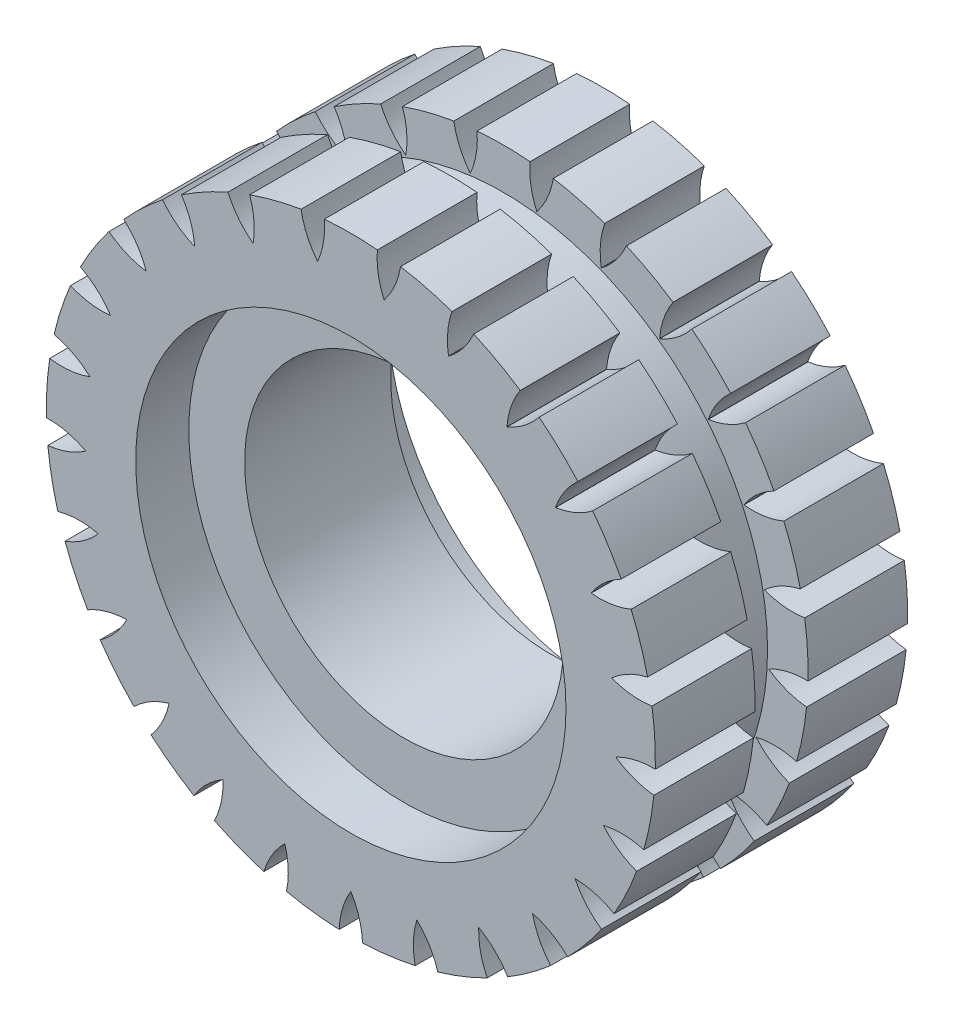
SolidWorks part; units mm, degrees
ref_plane "Ebene vorne" through (0, 0, 0) normal (0, 0, 1) x (1, 0, 0)
ref_plane "Ebene oben" through (0, 0, 0) normal (0, 1, 0) x (1, 0, 0)
ref_plane "Ebene rechts" through (0, 0, 0) normal (1, 0, 0) x (0, 0, -1)
sketch "Skizze1" plane through (0, 0, 0) normal (1, 0, 0) x (0, 0, -1)
  line L0 (-5.5, 0) -> (5.5, 0)
  line L1 (-19.3304, -12) -> (21.4195, -12) construction
  line L2 (0, 0) -> (0, 8) construction
  line L3 (-5.5, 0) -> (-5.5, 4.2)
  line L4 (-5.5, 4.2) -> (-9.5, 4.2)
  line L5 (-9.5, 4.2) -> (-9.5, 8)
  line L6 (-9.5, 8) -> (9.5, 8)
  line L7 (9.5, 4.2) -> (9.5, 8)
  line L8 (5.5, 4.2) -> (9.5, 4.2)
  line L9 (5.5, 0) -> (5.5, 4.2)
  dimension "D1" = 4.2
  dimension "D2" = 3.8
  dimension "D3" = 11
  dimension "D4" = 4
  dimension "D5" = 40
revolve "Rotation1" add sketch "Skizze1" angle 360 about L1
sketch "Skizze2" plane through (0, 0, 9.5) normal (0, 0, 1) x (1, 0, 0)
  line L1 (0, 18.2198) -> (0, 8) construction
  line L2 (0, 8) -> (0, -12) construction
  line L3 (-2, 10.8431) -> (-3.3426, 26.1783) construction
  line L5 (-14.9244, 9.7116) -> (-2, 10.8431) construction
  circle A1 centre (0, -12) radius 20 construction
  arc A76 (-2.5, 7.8431) -> (2.5, 7.8431) centre (0, -12) cw
  arc A77 (-2.5, 7.8431) -> (-2, 10.8431) centre (-8.0643, 10.3122) ccw
  arc A78 (-2, 10.8431) -> (2, 10.8431) centre (0, -12) cw
  arc A79 (2.5, 7.8431) -> (2, 10.8431) centre (8.0643, 10.3122) cw
  arc A80 (3.7437, 10.6229) -> (7.618, 9.6281) centre (0, -12) cw
  arc A81 (2.5133, 7.8415) -> (3.7437, 10.6229) centre (-2.2621, 11.6167) ccw
  arc A82 (2.5133, 7.8415) -> (7.3562, 6.598) centre (0, -12) cw
  arc A83 (7.3562, 6.598) -> (7.618, 9.6281) centre (13.3598, 7.6057) cw
  arc A84 (9.2522, 8.9811) -> (12.7574, 7.0541) centre (0, -12) cw
  arc A85 (7.3687, 6.5931) -> (9.2522, 8.9811) centre (3.6822, 11.4373) ccw
  arc A86 (7.3687, 6.5931) -> (11.7503, 4.1843) centre (0, -12) cw
  arc A87 (11.7503, 4.1843) -> (12.7574, 7.0541) centre (17.8158, 3.6673) cw
  arc A88 (14.1793, 6.021) -> (17.0951, 3.2828) centre (0, -12) cw
  arc A89 (11.7611, 4.1764) -> (14.1793, 6.021) centre (9.3951, 9.7853) ccw
  arc A90 (11.7611, 4.1764) -> (15.406, 0.7537) centre (0, -12) cw
  arc A91 (15.406, 0.7537) -> (17.0951, 3.2828) centre (21.1524, -1.2555) cw
  arc A92 (18.2154, 1.9286) -> (20.3588, -1.4487) centre (0, -12) cw
  arc A93 (15.4145, 0.7433) -> (18.2154, 1.9286) centre (14.5177, 6.7644) ccw
  arc A94 (15.4145, 0.7433) -> (18.0937, -3.4783) centre (0, -12) cw
  arc A95 (18.0937, -3.4783) -> (20.3588, -1.4487) centre (23.1599, -6.8534) cw
  arc A96 (21.1071, -3.039) -> (22.3431, -6.8432) centre (0, -12) cw
  arc A97 (18.0994, -3.4905) -> (21.1071, -3.039) centre (18.7281, 2.5644) ccw
  arc A98 (18.0994, -3.4905) -> (19.6445, -8.2458) centre (0, -12) cw
  arc A99 (19.6445, -8.2458) -> (22.3431, -6.8432) centre (23.7122, -12.7748) cw
  arc A100 (22.6725, -8.5696) -> (22.9236, -12.5617) centre (0, -12) cw
  arc A101 (19.647, -8.259) -> (22.6725, -8.5696) centre (21.7618, -2.5506) ccw
  arc A102 (19.647, -8.259) -> (19.961, -13.2491) centre (0, -12) cw
  arc A103 (19.961, -13.2491) -> (22.9236, -12.5617) centre (22.7745, -18.6474) cw
  arc A104 (22.8133, -14.3158) -> (22.0638, -18.245) centre (0, -12) cw
  arc A105 (19.9601, -13.2625) -> (22.8133, -14.3158) centre (23.4281, -8.2594) ccw
  arc A106 (19.9601, -13.2625) -> (19.0232, -18.174) centre (0, -12) cw
  arc A107 (19.0232, -18.174) -> (22.0638, -18.245) centre (20.4059, -24.1023) cw
  arc A108 (21.5206, -19.9165) -> (19.8175, -23.5358) centre (0, -12) cw
  arc A109 (19.0191, -18.1867) -> (21.5206, -19.9165) centre (23.6223, -14.2033) ccw
  arc A110 (19.0191, -18.1867) -> (16.8902, -22.7109) centre (0, -12) cw
  arc A111 (16.8902, -22.7109) -> (19.8175, -23.5358) centre (16.7551, -28.7969) cw
  arc A112 (18.8758, -25.0197) -> (16.3261, -28.1018) centre (0, -12) cw
  arc A113 (16.883, -22.7222) -> (18.8758, -25.0197) centre (22.3322, -20.0087) ccw
  arc A114 (16.883, -22.7222) -> (13.6958, -26.5748) centre (0, -12) cw
  arc A115 (13.6958, -26.5748) -> (16.3261, -28.1018) centre (12.0515, -32.436) cw
  arc A116 (15.0449, -29.3049) -> (11.8088, -31.6561) centre (0, -12) cw
  arc A117 (13.686, -26.584) -> (15.0449, -29.3049) centre (19.6389, -25.3109) ccw
  arc A118 (13.686, -26.584) -> (9.641, -29.5229) centre (0, -12) cw
  arc A119 (9.641, -29.5229) -> (11.8088, -31.6561) centre (6.5906, -34.791) cw
  arc A120 (10.2687, -32.5028) -> (6.5496, -33.9753) centre (0, -12) cw
  arc A121 (9.6292, -29.5294) -> (10.2687, -32.5028) centre (15.7117, -29.7767) ccw
  arc A122 (9.6292, -29.5294) -> (4.9803, -31.37) centre (0, -12) cw
  arc A123 (4.9803, -31.37) -> (6.5496, -33.9753) centre (0.7157, -35.714) cw
  arc A124 (4.8472, -34.4123) -> (0.8788, -34.9137) centre (0, -12) cw
  arc A125 (4.9673, -31.3733) -> (4.8472, -34.4123) centre (10.7972, -33.1255) ccw
  arc A126 (4.9673, -31.3733) -> (0.0067, -32) centre (0, -12) cw
  arc A127 (0.0067, -32) -> (0.8788, -34.9137) centre (-5.2042, -35.147) cw
  arc A128 (-0.8788, -34.9137) -> (-4.8472, -34.4123) centre (0, -12) cw
  arc A129 (-0.0067, -32) -> (-0.8788, -34.9137) centre (5.2042, -35.147) ccw
  arc A130 (-0.0067, -32) -> (-4.9673, -31.3733) centre (0, -12) cw
  arc A131 (-4.9673, -31.3733) -> (-4.8472, -34.4123) centre (-10.7972, -33.1255) cw
  arc A132 (-6.5496, -33.9753) -> (-10.2687, -32.5028) centre (0, -12) cw
  arc A133 (-4.9803, -31.37) -> (-6.5496, -33.9753) centre (-0.7157, -35.714) ccw
  arc A134 (-4.9803, -31.37) -> (-9.6292, -29.5294) centre (0, -12) cw
  arc A135 (-9.6292, -29.5294) -> (-10.2687, -32.5028) centre (-15.7117, -29.7767) cw
  arc A136 (-11.8088, -31.6561) -> (-15.0449, -29.3049) centre (0, -12) cw
  arc A137 (-9.641, -29.5229) -> (-11.8088, -31.6561) centre (-6.5906, -34.791) ccw
  arc A138 (-9.641, -29.5229) -> (-13.686, -26.584) centre (0, -12) cw
  arc A139 (-13.686, -26.584) -> (-15.0449, -29.3049) centre (-19.6389, -25.3109) cw
  arc A140 (-16.3261, -28.1018) -> (-18.8758, -25.0197) centre (0, -12) cw
  arc A141 (-13.6958, -26.5748) -> (-16.3261, -28.1018) centre (-12.0515, -32.436) ccw
  arc A142 (-13.6958, -26.5748) -> (-16.883, -22.7222) centre (0, -12) cw
  arc A143 (-16.883, -22.7222) -> (-18.8758, -25.0197) centre (-22.3322, -20.0087) cw
  arc A144 (-19.8175, -23.5358) -> (-21.5206, -19.9165) centre (0, -12) cw
  arc A145 (-16.8902, -22.7109) -> (-19.8175, -23.5358) centre (-16.7551, -28.7969) ccw
  arc A146 (-16.8902, -22.7109) -> (-19.0191, -18.1867) centre (0, -12) cw
  arc A147 (-19.0191, -18.1867) -> (-21.5206, -19.9165) centre (-23.6223, -14.2033) cw
  arc A148 (-22.0638, -18.245) -> (-22.8133, -14.3158) centre (0, -12) cw
  arc A149 (-19.0232, -18.174) -> (-22.0638, -18.245) centre (-20.4059, -24.1023) ccw
  arc A150 (-19.0232, -18.174) -> (-19.9601, -13.2625) centre (0, -12) cw
  arc A151 (-19.9601, -13.2625) -> (-22.8133, -14.3158) centre (-23.4281, -8.2594) cw
  arc A152 (-22.9236, -12.5617) -> (-22.6725, -8.5696) centre (0, -12) cw
  arc A153 (-19.961, -13.2491) -> (-22.9236, -12.5617) centre (-22.7745, -18.6474) ccw
  arc A154 (-19.961, -13.2491) -> (-19.647, -8.259) centre (0, -12) cw
  arc A155 (-19.647, -8.259) -> (-22.6725, -8.5696) centre (-21.7618, -2.5506) cw
  arc A156 (-22.3431, -6.8432) -> (-21.1071, -3.039) centre (0, -12) cw
  arc A157 (-19.6445, -8.2458) -> (-22.3431, -6.8432) centre (-23.7122, -12.7748) ccw
  arc A158 (-19.6445, -8.2458) -> (-18.0994, -3.4905) centre (0, -12) cw
  arc A159 (-18.0994, -3.4905) -> (-21.1071, -3.039) centre (-18.7281, 2.5644) cw
  arc A160 (-20.3588, -1.4487) -> (-18.2154, 1.9286) centre (0, -12) cw
  arc A161 (-18.0937, -3.4783) -> (-20.3588, -1.4487) centre (-23.1599, -6.8534) ccw
  arc A162 (-18.0937, -3.4783) -> (-15.4145, 0.7433) centre (0, -12) cw
  arc A163 (-15.4145, 0.7433) -> (-18.2154, 1.9286) centre (-14.5177, 6.7644) cw
  arc A164 (-17.0951, 3.2828) -> (-14.1793, 6.021) centre (0, -12) cw
  arc A165 (-15.406, 0.7537) -> (-17.0951, 3.2828) centre (-21.1524, -1.2555) ccw
  arc A166 (-15.406, 0.7537) -> (-11.7611, 4.1764) centre (0, -12) cw
  arc A167 (-11.7611, 4.1764) -> (-14.1793, 6.021) centre (-9.3951, 9.7853) cw
  arc A168 (-12.7574, 7.0541) -> (-9.2522, 8.9811) centre (0, -12) cw
  arc A169 (-11.7503, 4.1843) -> (-12.7574, 7.0541) centre (-17.8158, 3.6673) ccw
  arc A170 (-11.7503, 4.1843) -> (-7.3687, 6.5931) centre (0, -12) cw
  arc A171 (-7.3687, 6.5931) -> (-9.2522, 8.9811) centre (-3.6822, 11.4373) cw
  arc A172 (-7.618, 9.6281) -> (-3.7437, 10.6229) centre (0, -12) cw
  arc A173 (-7.3562, 6.598) -> (-7.618, 9.6281) centre (-13.3598, 7.6057) ccw
  arc A174 (-7.3562, 6.598) -> (-2.5133, 7.8415) centre (0, -12) cw
  arc A175 (-2.5133, 7.8415) -> (-3.7437, 10.6229) centre (2.2621, 11.6167) cw
  point P160 (0, -12)
  dimension "D3" = 3
  dimension "D1" = 5
  dimension "D2" = 4
  dimension "D4" = 25
extrude "Aufsatz-Linear austragen1" add sketch "Skizze2" against normal through all
sketch "Skizze3" plane through (0, 0, 0) normal (1, 0, 0) x (0, 0, -1)
  line L0 (0, 7.8415) -> (0, 0) construction
  line L1 (-2, 11.3431) -> (2, 11.3431)
  line L2 (-2, 11.3431) -> (-2, 7.8415)
  line L3 (-2, 7.8415) -> (2, 7.8415)
  line L4 (2, 11.3431) -> (2, 7.8415)
  line L6 (9.5, 10.8431) -> (-9.5, 10.8431) construction
  line L7 (-15.257, -12.0353) -> (27.6114, -12.0353) construction
  line L8 (-15.257, 10.8431) -> (-15.257, -34.9137) construction
  line L9 (-15.257, -34.9137) -> (-9.5, -34.9137) construction
  line L10 (-15.257, 10.8431) -> (-9.5, 10.8431) construction
  line L12 (9.5, 7.8415) -> (-9.5, 7.8415) construction
  dimension "D1" = 4
  dimension "D2" = 0.5
revolve "Schnitt-Rotation2" cut sketch "Skizze3" angle 360 about L7
